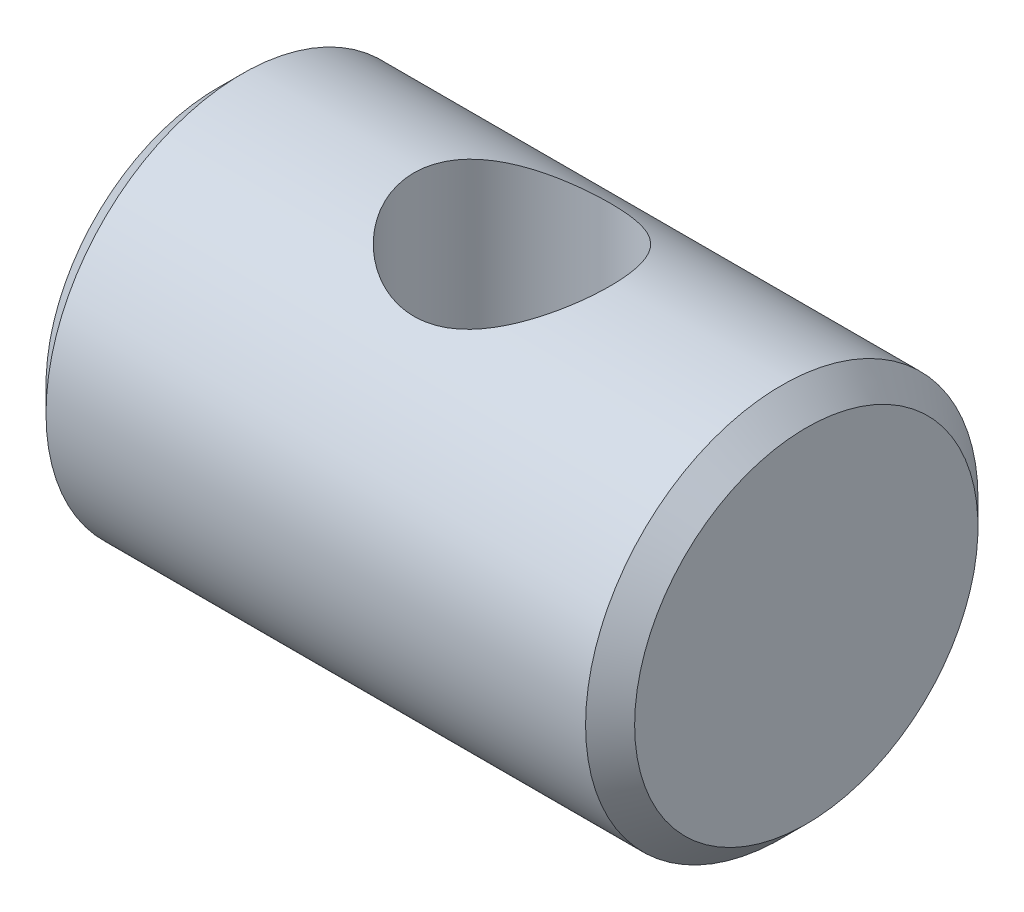
SolidWorks part; units mm, degrees
material "AISI 4340 Stal normalizowana"
ref_plane "Płaszczyzna XY" through (0, 0, 0) normal (0, 0, 1) x (1, 0, 0)
ref_plane "Płaszczyzna XZ" through (0, 0, 0) normal (0, 1, 0) x (1, 0, 0)
ref_plane "Płaszczyzna YZ" through (0, 0, 0) normal (1, 0, 0) x (0, 0, -1)
sketch "Szkic1" plane through (0, 0, 0) normal (0, 0, 1) x (1, 0, 0)
  line L0 (0, 0) -> (24, 0)
  line L1 (24, 0) -> (24, 8)
  line L2 (24, 8) -> (0, 8)
  line L3 (0, 8) -> (0, 0)
  line L4 (12, 0) -> (12, 28.6488) construction
  point P3 (12, 0)
  dimension "D1" = 8
  dimension "D2" = 24
revolve "Obrót1" add sketch "Szkic1" angle 360 about L0
sketch "Szkic2" plane through (0, 0, 0) normal (0, 1, 0) x (1, 0, 0)
  circle A0 centre (12, 0) radius 4
  dimension "D1" = 8
  dimension "D2" = 12
extrude "Wytnij-wyciągnięcie1" cut sketch "Szkic2" against normal up to next and the other way up to next
chamfer "Sfazowanie1" distance 1 angle 45 2 edges at (24, 0, 8) (0, 0, 8)
ref_point "Punkt1"
